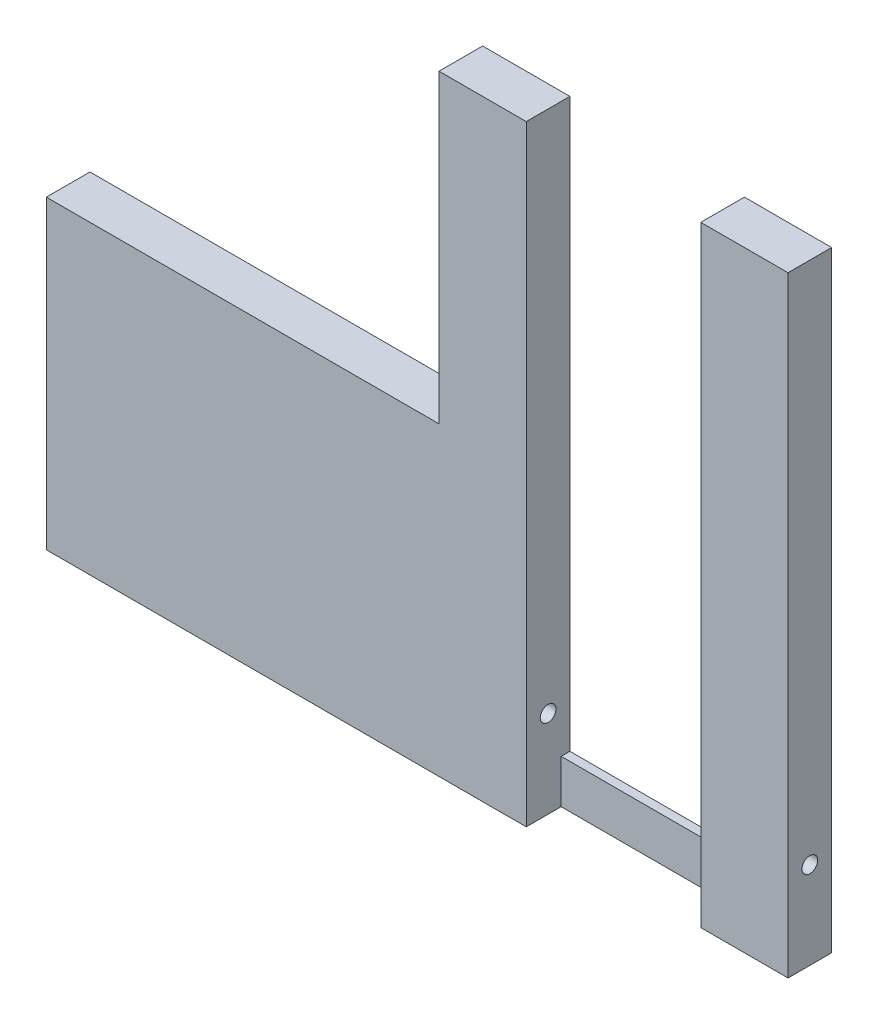
SolidWorks part; units mm, degrees
ref_plane "Front Plane" through (0, 0, 0) normal (0, 0, 1) x (1, 0, 0)
ref_plane "Top Plane" through (0, 0, 0) normal (0, 1, 0) x (1, 0, 0)
ref_plane "Right Plane" through (0, 0, 0) normal (1, 0, 0) x (0, 0, -1)
sketch "Sketch2" plane through (0, 0, 0) normal (0, 0, 1) x (1, 0, 0)
  line L1 (0, 0) -> (4, 0)
  line L2 (0, 0) -> (0, 28)
  line L3 (0, 28) -> (4, 28)
  line L4 (4, 0) -> (4, 28)
  line L5 (12, 0) -> (16, 0)
  line L6 (12, 0) -> (12, 28)
  line L7 (12, 28) -> (16, 28)
  line L8 (16, 0) -> (16, 28)
  dimension "D1" = 4
  dimension "D2" = 28
  dimension "D3" = 28
  dimension "D4" = 4
  dimension "D5" = 8
extrude "Boss-Extrude1" add sketch "Sketch2" along normal blind 2
sketch "Sketch3" plane through (0, 0, 0) normal (0, 0, -1) x (-1, 0, 0)
  line L0 (-16, 0) -> (-16, 28) construction
  line L1 (0, 0) -> (-16, 0)
  line L2 (0, 0) -> (0, 2)
  line L3 (0, 2) -> (-16, 2)
  line L4 (-16, 0) -> (-16, 2)
  dimension "D1" = 2
extrude "Boss-Extrude2" add sketch "Sketch3" against normal blind 0.4
sketch "Sketch6" plane through (16, 0, 0) normal (1, 0, 0) x (0, 0, -1)
  line L0 (-2, 0) -> (-2, 28) construction
  line L1 (0, 0) -> (-2, 0) construction
  circle A0 centre (-1, 4) radius 0.36
  dimension "D1" = 0.72
  dimension "D2" = 1
  dimension "D3" = 4
sketch "Sketch7" plane through (0, 0, 0) normal (-1, 0, 0) x (0, 0, 1)
  line L0 (2, 28) -> (2, 0) construction
  line L1 (0, 0) -> (2, 0)
  line L2 (0, 0) -> (0, 14)
  line L3 (0, 14) -> (2, 14)
  line L4 (2, 0) -> (2, 14)
  dimension "D1" = 14
extrude "Boss-Extrude3" add sketch "Sketch7" along normal blind 18
extrude "Cut-Extrude1" cut sketch "Sketch6" against normal through all
